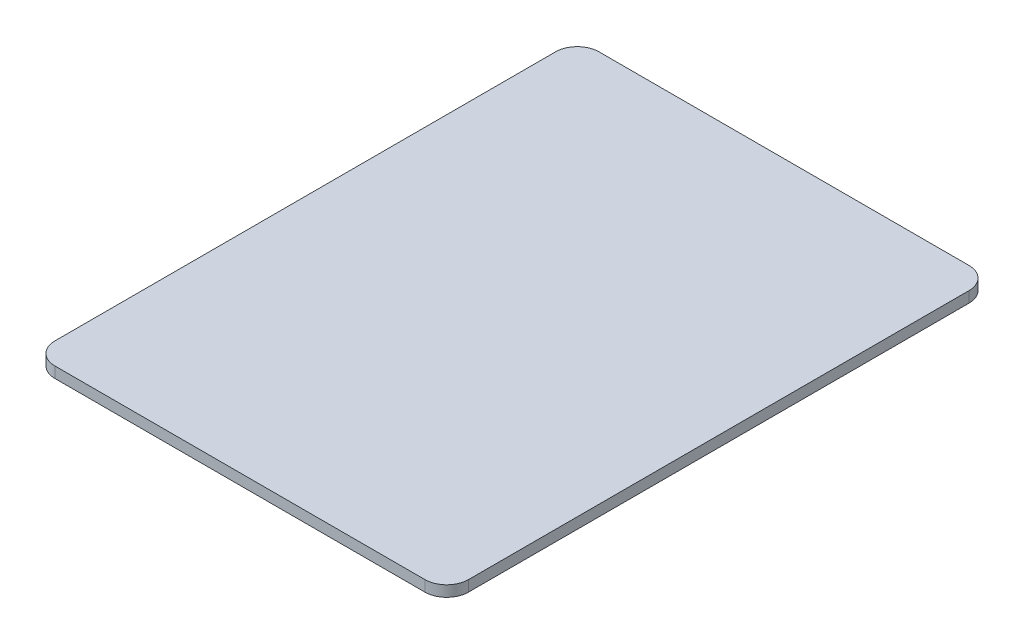
SolidWorks part; units mm, degrees
material "ABS"
ref_plane "Alzado" through (0, 0, 0) normal (0, 0, 1) x (1, 0, 0)
ref_plane "Planta" through (0, 0, 0) normal (0, 1, 0) x (1, 0, 0)
ref_plane "Vista lateral" through (0, 0, 0) normal (1, 0, 0) x (0, 0, -1)
sketch "Croquis1" plane through (0, 0, 0) normal (0, 1, 0) x (1, 0, 0)
  line L1 (0, 0) -> (190, 0)
  line L2 (0, 0) -> (0, 250)
  line L3 (0, 250) -> (190, 250)
  line L4 (190, 0) -> (190, 250)
  dimension "D1" = 250
  dimension "D2" = 190
extrude "Saliente-Extruir1" add sketch "Croquis1" along normal blind 5
fillet "Redondeo1" radius 10 4 edges at (0, 2.5, -250) (190, 2.5, -250) (0, 2.5, 0) (190, 2.5, 0)
sketch "Croquis2" plane through (0, 0, 0) normal (0, -1, 0) x (1, 0, 0)
  line L0 (190, -10) -> (190, -240) construction
  line L1 (20, -10) -> (170, -10)
  line L2 (20, -10) -> (20, -240)
  line L3 (20, -240) -> (170, -240)
  line L4 (170, -10) -> (170, -240)
  line L5 (20, -10) -> (170, -240) construction
  line L6 (20, -240) -> (170, -10) construction
  line L7 (180, -250) -> (10, -250) construction
  point P0 (95, -125)
  point P5 (94.4696, -128.0054)
  point P6 (0, 0)
  point P9 (190, -125)
  point P10 (0, 0)
  point P13 (95, -250)
  dimension "D1" = 150
  dimension "D2" = 230
extrude "Saliente-Extruir2" add sketch "Croquis2" along normal blind 10
